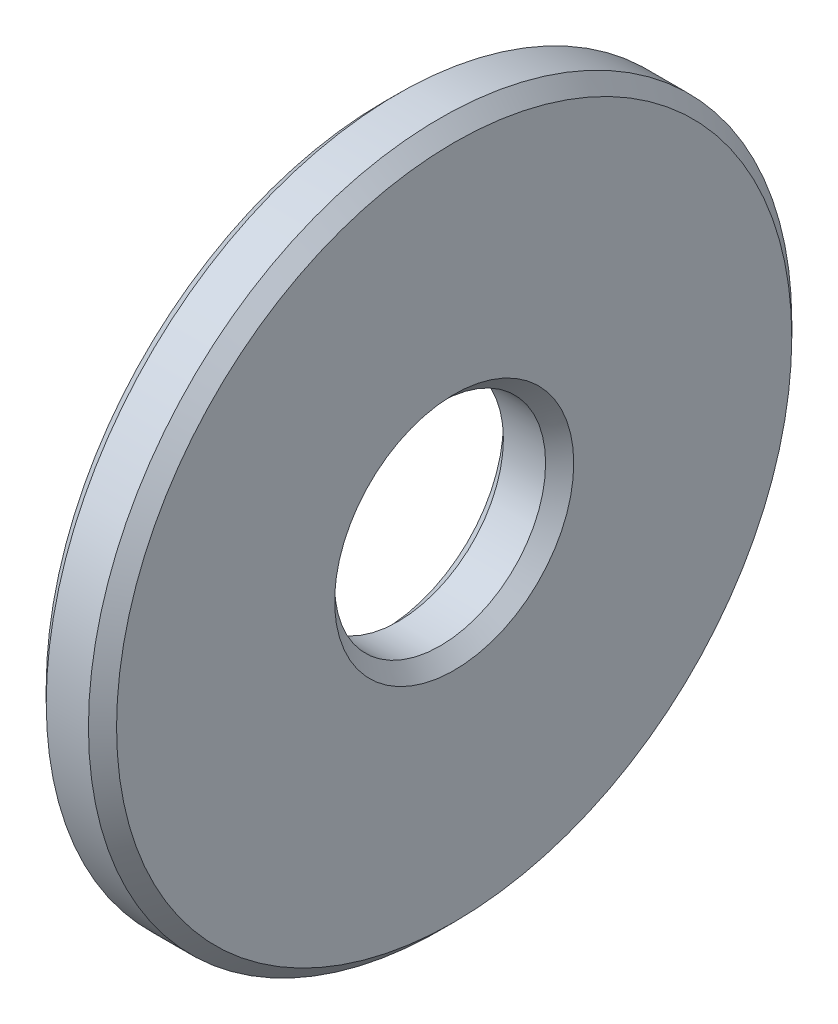
SolidWorks part; units mm, degrees
ref_plane "Front Plane" through (0, 0, 0) normal (0, 0, 1) x (1, 0, 0)
ref_plane "Top Plane" through (0, 0, 0) normal (0, 1, 0) x (1, 0, 0)
ref_plane "Right Plane" through (0, 0, 0) normal (1, 0, 0) x (0, 0, -1)
sketch "Sketch1" plane through (0, 0, 0) normal (0, 0, 1) x (1, 0, 0)
  line L0 (0, 4.8) -> (0, 1.7)
  line L1 (0, 1.7) -> (0.2, 1.5)
  line L2 (0.2, 1.5) -> (0.8, 1.5)
  line L3 (0.8, 1.5) -> (1, 1.7)
  line L4 (1, 1.7) -> (1, 4.8)
  line L5 (1, 4.8) -> (0.8, 5)
  line L6 (0.8, 5) -> (0.2, 5)
  line L7 (0.2, 5) -> (0, 4.8)
  line L8 (0, 0) -> (1, 0) construction
revolve "Revolve1" add sketch "Sketch1" angle 360 about L8
